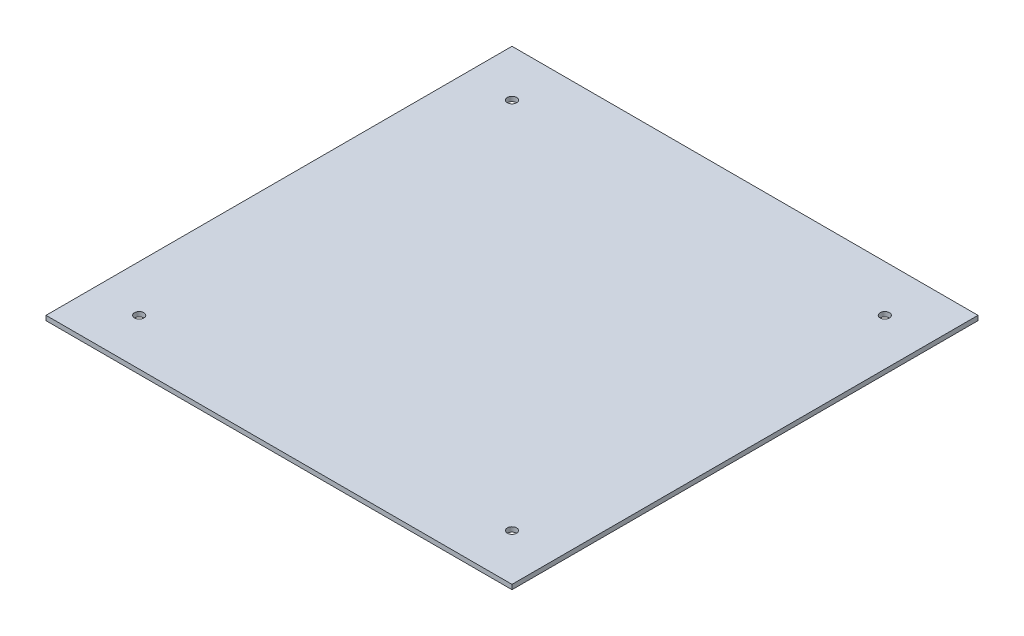
SolidWorks part; units mm, degrees
ref_plane "Front Plane" through (0, 0, 0) normal (0, 0, 1) x (1, 0, 0)
ref_plane "Top Plane" through (0, 0, 0) normal (0, 1, 0) x (1, 0, 0)
ref_plane "Right Plane" through (0, 0, 0) normal (1, 0, 0) x (0, 0, -1)
sketch "Sketch2" plane through (0, 0, 0) normal (0, 1, 0) x (1, 0, 0)
  line L1 (-250, 250) -> (250, 250)
  line L2 (-250, 250) -> (-250, -250)
  line L3 (-250, -250) -> (250, -250)
  line L4 (250, 250) -> (250, -250)
  line L5 (-250, 250) -> (250, -250) construction
  line L6 (-250, -250) -> (250, 250) construction
  point P0 (0, 0)
  dimension "D1" = 500
extrude "Boss-Extrude1" add sketch "Sketch2" along normal blind 5
sketch "Sketch3" plane through (0, 5, 0) normal (0, 1, 0) x (1, 0, 0)
  line L0 (250, -250) -> (250, 250) construction
  line L1 (-250, 250) -> (-250, -250) construction
  line L2 (250, 250) -> (-250, 250) construction
  line L3 (-250, -250) -> (250, -250) construction
  circle A0 centre (-200, 200) radius 5
  circle A1 centre (-200, -200) radius 5
  circle A2 centre (200, 200) radius 5
  circle A3 centre (200, -200) radius 5
  dimension "D5" = 10
  dimension "D1" = 50
  dimension "D2" = 50
  dimension "D3" = 50
  dimension "D4" = 50
extrude "Cut-Extrude1" cut sketch "Sketch3" against normal blind 10
